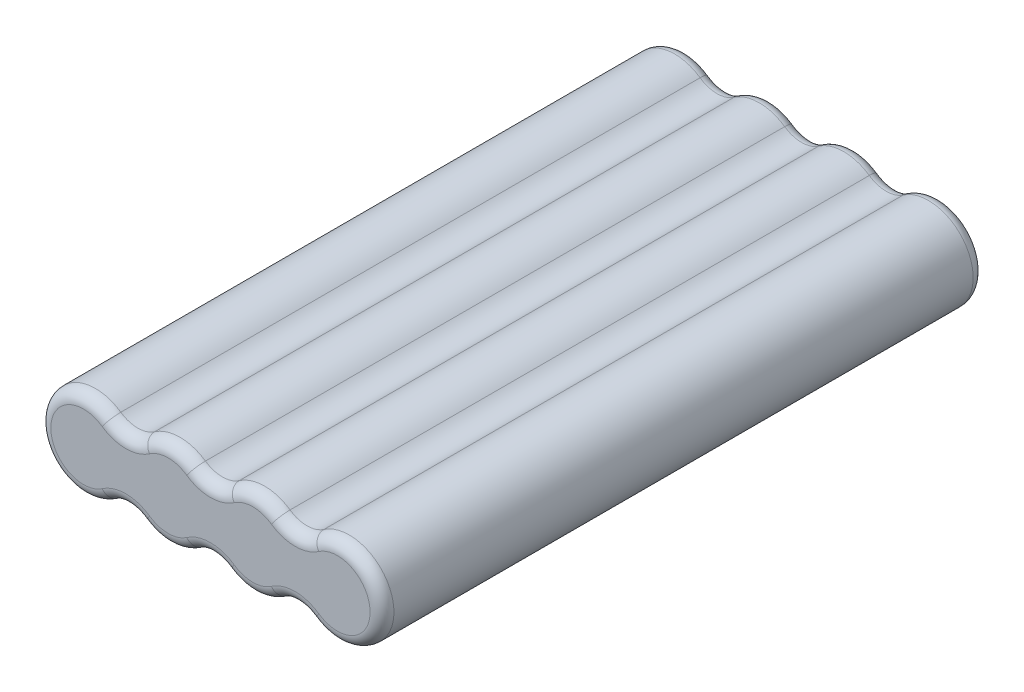
SolidWorks part; units mm, degrees
ref_plane "Front Plane" through (0, 0, 0) normal (0, 0, 1) x (1, 0, 0)
ref_plane "Top Plane" through (0, 0, 0) normal (0, 1, 0) x (1, 0, 0)
ref_plane "Right Plane" through (0, 0, 0) normal (1, 0, 0) x (0, 0, -1)
sketch "Sketch1" plane through (0, 0, 0) normal (0, 0, 1) x (1, 0, 0)
  line L0 (-21.329, 0) -> (-7.1097, 0) construction
  line L1 (-7.1097, 0) -> (7.1097, 0) construction
  line L2 (7.1097, 0) -> (21.329, 0) construction
  arc A0 (-17.0632, 6.1687) -> (-17.0632, -6.1687) centre (-21.329, 0) ccw
  arc A1 (-11.3755, -6.1687) -> (-2.8439, -6.1687) centre (-7.1097, 0) ccw
  arc A2 (2.8439, -6.1687) -> (11.3755, -6.1687) centre (7.1097, 0) ccw
  arc A3 (17.0632, -6.1687) -> (17.0632, 6.1687) centre (21.329, 0) ccw
  arc A4 (-2.8439, 6.1687) -> (-11.3755, 6.1687) centre (-7.1097, 0) ccw
  arc A5 (11.3755, 6.1687) -> (2.8439, 6.1687) centre (7.1097, 0) ccw
  arc A6 (17.0632, -6.1687) -> (11.3755, -6.1687) centre (14.2193, -10.2812) ccw
  arc A7 (2.8439, -6.1687) -> (-2.8439, -6.1687) centre (0, -10.2812) ccw
  arc A8 (-11.3755, -6.1687) -> (-17.0632, -6.1687) centre (-14.2193, -10.2812) ccw
  arc A9 (11.3755, 6.1687) -> (17.0632, 6.1687) centre (14.2193, 10.2812) ccw
  arc A10 (-2.8439, 6.1687) -> (2.8439, 6.1687) centre (0, 10.2812) ccw
  arc A11 (-11.3755, 6.1687) -> (-17.0632, 6.1687) centre (-14.2193, 10.2812) cw
  point P8 (-28.829, 0)
  point P9 (28.829, 0)
  dimension "D1" = 15
  dimension "D3" = 5
  dimension "D2" = 57.658
extrude "Boss-Extrude1" add sketch "Sketch1" along normal mid plane 101.346
fillet "Fillet1" radius 2 24 edges at (28.829, 0, -50.673) (14.2193, 5.2812, -50.673) (7.1097, 7.5, -50.673) (0, 5.2812, -50.673) (-7.1097, 7.5, -50.673) (-14.2193, 5.2812, -50.673) (-28.829, 0, -50.673) (-14.2193, -5.2812, -50.673) (-7.1097, -7.5, -50.673) (0, -5.2812, -50.673) (7.1097, -7.5, -50.673) (14.2193, -5.2812, -50.673) (7.1097, -7.5, 50.673) (0, -5.2812, 50.673) (-7.1097, -7.5, 50.673) (-14.2193, -5.2812, 50.673) (-28.829, 0, 50.673) (-14.2193, 5.2812, 50.673) (-7.1097, 7.5, 50.673) (0, 5.2812, 50.673) (7.1097, 7.5, 50.673) (14.2193, 5.2812, 50.673) (28.829, 0, 50.673) (14.2193, -5.2812, 50.673)
ref_plane "Plane1" through (0, 0, 0) normal (0, 1, 0) x (1, 0, 0)
ref_plane "Plane2" through (28.829, 0, 0) normal (1, 0, 0) x (0, 0, -1)
ref_plane "Plane3" through (-28.829, 0, 0) normal (-1, 0, 0) x (0, 0, 1)
